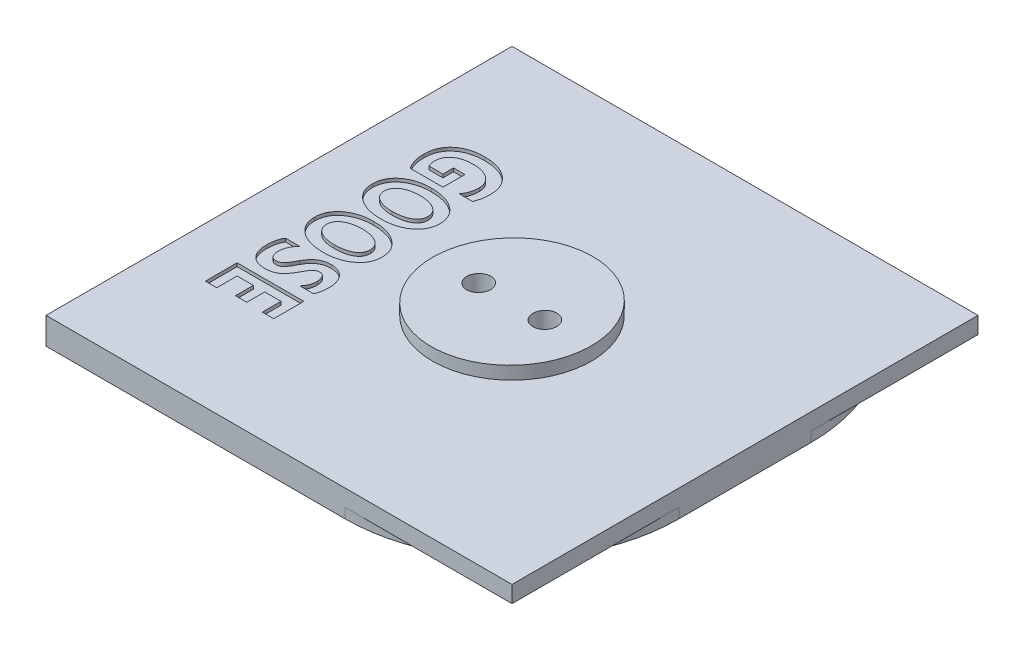
SolidWorks part; units mm, degrees
ref_plane "Front Plane" through (0, 0, 0) normal (0, 0, 1) x (1, 0, 0)
ref_plane "Top Plane" through (0, 0, 0) normal (0, 1, 0) x (1, 0, 0)
ref_plane "Right Plane" through (0, 0, 0) normal (1, 0, 0) x (0, 0, -1)
sketch "Sketch1" plane through (0, 0, 0) normal (0, 1, 0) x (1, 0, 0)
  line L1 (0, 0) -> (69.85, 0)
  line L2 (0, 0) -> (0, 69.85)
  line L3 (0, 69.85) -> (69.85, 69.85)
  line L4 (69.85, 0) -> (69.85, 69.85)
  dimension "D1" = 69.85
extrude "Boss-Extrude1" add sketch "Sketch1" along normal blind 4
sketch "Sketch2" plane through (0, 4, 0) normal (0, 1, 0) x (1, 0, 0)
  line L0 (0, 0) -> (69.85, 0) construction
  line L9 (0, 0) -> (34.925, 0) construction
  line L14 (0, 0) -> (0, 34.925) construction
  line L15 (0, 34.925) -> (34.925, 34.925) construction
  line L16 (34.925, 0) -> (34.925, 34.925) construction
  circle A0 centre (34.925, 34.925) radius 11.9062
  point P7 (34.925, 0)
  dimension "D1" = 23.8125
extrude "Boss-Extrude2" add sketch "Sketch2" along direction (0, -1, 0) on the side of the normal blind 2
sketch "Sketch4" plane through (0, 0, 0) normal (0, 0, -1) x (-1, 0, 0)
  line L3 (-46.8312, 6) -> (-24.9423, 6) construction
  line L4 (-23.0187, 6) -> (-46.8312, 6) construction
  line L5 (-46.8312, 6) -> (-23.0187, 6)
  line L6 (-23.0187, 6) -> (-23.0187, 5.5844)
  line L7 (-26.2709, 5.6411) -> (-45.4903, 5.9766) construction
  line L8 (-46.8312, 6) -> (-23.0187, 5.5844)
  dimension "D1" = 1
extrude "Cut-Extrude2" cut sketch "Sketch4" along normal through all
sketch "Sketch5" plane through (-0.0904, 5.181, 0) normal (-0.0175, 0.9998, 0) x (0.9998, 0.0175, 0)
  line L0 (23.1127, 34.925) -> (46.9288, 34.925) construction
  ellipse E0 centre (35.0208, 34.925) end of major axis (23.1127, 34.925) minor radius 11.9062 construction
sketch "Sketch3" plane through (0.0071, 5.1827, 0) normal (-0.0175, 0.9998, 0) x (0.9998, 0.0175, 0)
  line L0 (-0.0278, 34.925) -> (69.8116, 34.925) construction
  line L1 (-0.0278, 69.85) -> (-0.0278, 0) construction
  line L2 (69.8116, 0) -> (69.8116, 69.85) construction
  line L3 (31.7169, 34.925) -> (38.0669, 34.925) construction
  line L4 (28.145, 34.925) -> (41.6388, 34.925) construction
  line L5 (28.145, 34.925) -> (28.145, 44.7143) construction
  line L6 (41.6388, 34.925) -> (41.6388, 44.7143) construction
  line L7 (28.145, 44.7143) -> (41.6388, 44.7143) construction
  line L8 (31.7169, 34.925) -> (31.7169, 44.7143) construction
  line L9 (38.0669, 34.925) -> (38.0669, 44.7143) construction
  line L10 (31.7169, 44.7143) -> (38.0669, 44.7143) construction
  circle A0 centre (29.931, 34.925) radius 1.7859
  circle A1 centre (39.8528, 34.925) radius 1.7859
  ellipse E0 centre (34.9232, 34.925) end of major axis (23.0151, 34.925) minor radius 11.9062 construction
  point P10 (34.8919, 44.7143)
  point P22 (34.8919, 34.925)
  dimension "D1" = 6.35
  dimension "D2" = 13.4937
extrude "Cut-Extrude1" cut sketch "Sketch3" against normal up to surface (5.6747 mm away)
sketch "Sketch6" plane through (0, 4, 0) normal (0, 1, 0) x (1, 0, 0)
  line L0 (7.5, 69.85) -> (7.5, 0) construction
  line L1 (69.85, 69.85) -> (0, 69.85) construction
  line L2 (0, 0) -> (69.85, 0) construction
  line L3 (17.5, 69.85) -> (17.5, 0) construction
  line L4 (7.5, 69.85) -> (17.5, 69.85) construction
  line L5 (23.0187, 34.925) -> (0, 34.925) construction
  line L6 (0, 69.85) -> (0, 0) construction
  circle A0 centre (34.925, 34.925) radius 11.9062 construction
  text T0 "<b>GOOSE</b>" font "@Microsoft YaHei" height 10
  point P15 (12.5, 69.85)
  dimension "D1" = 10
  dimension "D2" = 12.5
extrude "Cut-Extrude3" cut sketch "Sketch6" against normal blind 0.5
sketch "Sketch8" plane through (0, 0, 0) normal (0, -1, 0) x (1, 0, 0)
  line L0 (69.85, 0) -> (44.85, 0)
  line L1 (0, 0) -> (69.85, 0) construction
  line L2 (69.85, -25) -> (69.85, 0)
  line L3 (69.85, 0) -> (69.85, -69.85) construction
  arc A0 (44.85, 0) -> (69.85, -25) centre (44.85, -25) cw
  point P7 (69.85, -16.9898)
  point P8 (69.85, -19.429)
  point P11 (48.2688, 0)
  point P12 (69.85, 0)
  point P13 (49.321, -20.529)
  dimension "D1" = 25
extrude "Cut-Extrude4" cut sketch "Sketch8" against normal blind 1.5
ref_plane "Plane1" through (0, 0, -34.925) normal (0, 0, 1) x (1, 0, 0)
mirror "Mirror1" about plane through (0, 0, -34.925) normal (0, 0, 1) of "Cut-Extrude4"
equation "\".0q\"=0"
